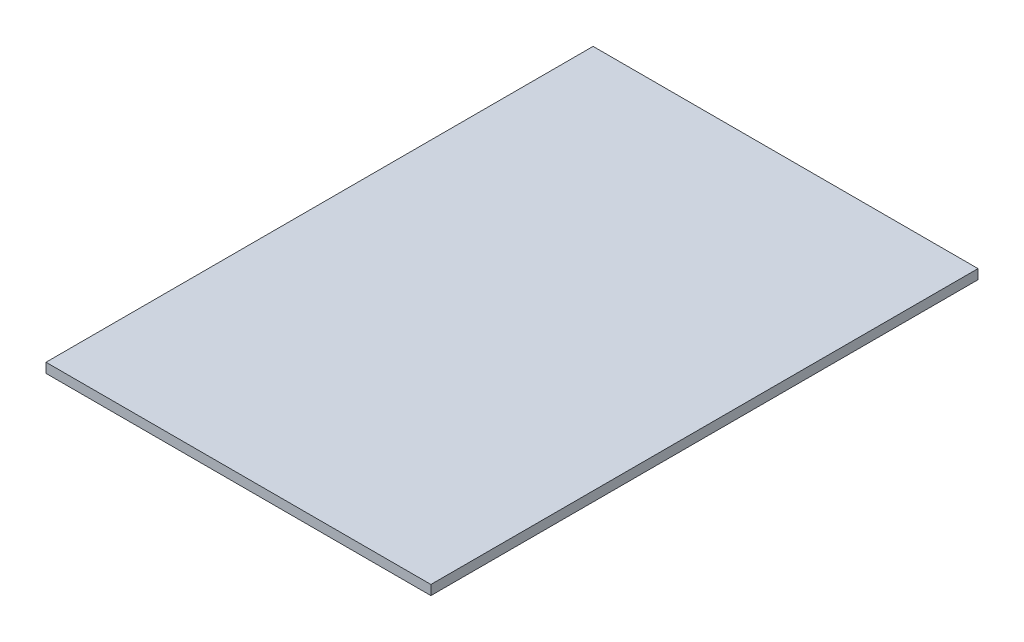
SolidWorks part; units mm, degrees
ref_plane "Front Plane" through (0, 0, 0) normal (0, 0, 1) x (1, 0, 0)
ref_plane "Top Plane" through (0, 0, 0) normal (0, 1, 0) x (1, 0, 0)
ref_plane "Right Plane" through (0, 0, 0) normal (1, 0, 0) x (0, 0, -1)
sketch "Sketch1" plane through (0, 0, 0) normal (0, 1, 0) x (1, 0, 0)
  line L1 (0, 0) -> (79.5, 0)
  line L2 (0, 0) -> (0, 113)
  line L3 (0, 113) -> (79.5, 113)
  line L4 (79.5, 0) -> (79.5, 113)
  dimension "D1" = 79.5
  dimension "D2" = 113
extrude "Boss-Extrude1" add sketch "Sketch1" along normal blind 2
